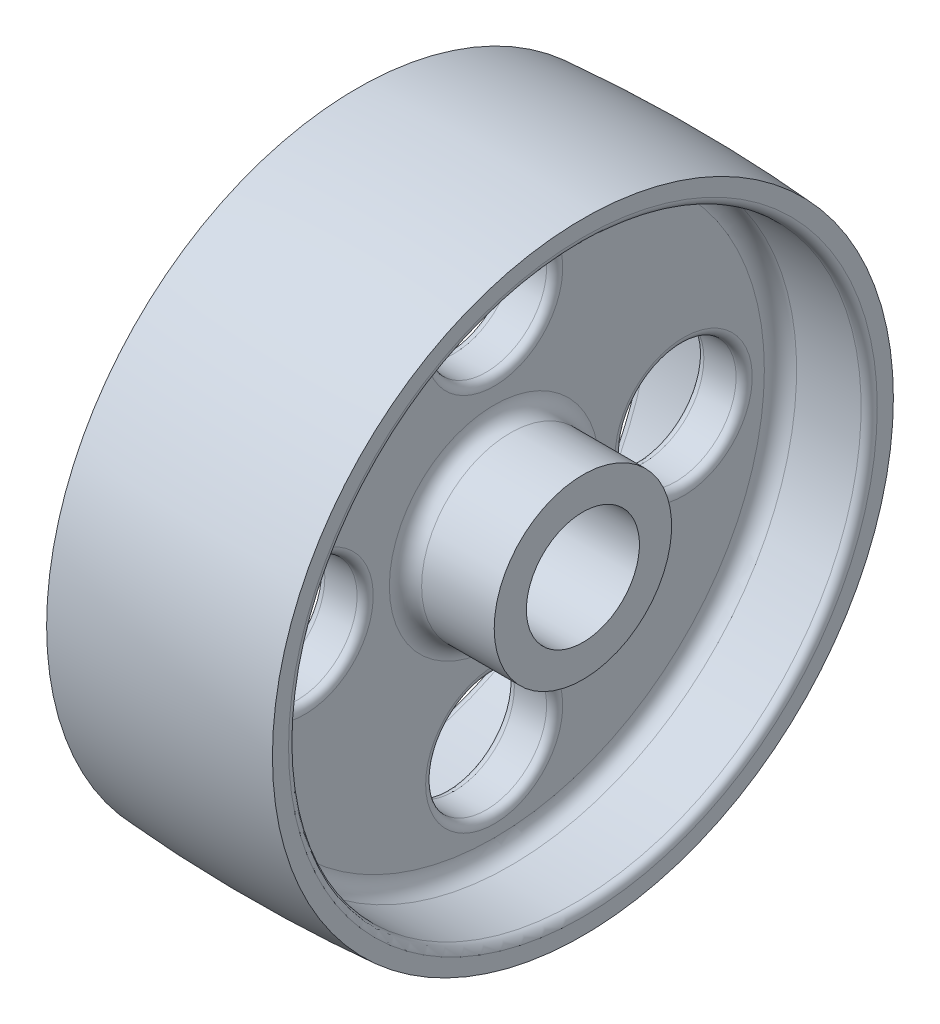
SolidWorks part; units mm, degrees
ref_plane "Front Plane" through (0, 0, 0) normal (0, 0, 1) x (1, 0, 0)
ref_plane "Top Plane" through (0, 0, 0) normal (0, 1, 0) x (1, 0, 0)
ref_plane "Right Plane" through (0, 0, 0) normal (1, 0, 0) x (0, 0, -1)
sketch "Sketch1" plane through (0, 0, 0) normal (0, 0, 1) x (1, 0, 0)
  line L0 (0, 0) -> (22.225, 0) construction
  line L2 (22.225, 11.1252) -> (22.225, 17.4625)
  line L3 (22.225, 17.4625) -> (7.9375, 17.4625)
  line L4 (4.7625, 20.6375) -> (4.7625, 53.1812)
  line L5 (7.9375, 56.3562) -> (20.6375, 56.3562)
  line L6 (22.225, 57.9438) -> (22.225, 61.1187)
  line L7 (0, 0) -> (0, 61.9125) construction
  line L8 (-22.225, 57.9438) -> (-22.225, 61.1187)
  line L9 (-7.9375, 56.3562) -> (-20.6375, 56.3562)
  line L10 (-4.7625, 20.6375) -> (-4.7625, 53.1812)
  line L11 (-22.225, 17.4625) -> (-7.9375, 17.4625)
  line L15 (-22.225, 11.1252) -> (22.225, 11.1252)
  line L17 (-22.225, 11.1252) -> (-22.225, 17.4625)
  arc A0 (-22.225, 61.1187) -> (22.225, 61.1187) centre (0, -249.6344) cw
  arc A1 (-7.9375, 56.3562) -> (-4.7625, 53.1812) centre (-7.9375, 53.1812) cw
  arc A2 (4.7625, 53.1812) -> (7.9375, 56.3562) centre (7.9375, 53.1812) cw
  arc A3 (7.9375, 17.4625) -> (4.7625, 20.6375) centre (7.9375, 20.6375) cw
  arc A4 (-4.7625, 20.6375) -> (-7.9375, 17.4625) centre (-7.9375, 20.6375) cw
  arc A5 (20.6375, 56.3562) -> (22.225, 57.9438) centre (20.6375, 57.9437) ccw
  arc A6 (-22.225, 57.9438) -> (-20.6375, 56.3562) centre (-20.6375, 57.9437) ccw
  point P16 (0, 0)
  point P20 (-4.7625, 56.3562)
  point P23 (4.7625, 56.3562)
  point P26 (4.7625, 17.4625)
  point P29 (-4.7625, 17.4625)
  point P34 (22.225, 56.3562)
  point P37 (-22.225, 56.3562)
  dimension "D8" = 3.175
  dimension "D11" = 1.5875
  dimension "D1" = 22.225
  dimension "D2" = 11.1252
  dimension "D3" = 17.4625
  dimension "D4" = 9.525
  dimension "D5" = 61.9125
  dimension "D6" = 0.7937
  dimension "D7" = 4.7625
revolve "Revolve1" add sketch "Sketch1" angle 360 about L0
sketch "Sketch2" plane through (0, 0, 0) normal (1, 0, 0) x (0, 0, -1)
  line L0 (0, 61.9125) -> (0, -61.9125) construction
  circle A0 centre (0, 0) radius 61.9125 construction
  circle A1 centre (0, 37.3062) radius 11.9063
  circle A3 centre (37.3062, 0) radius 11.9063
  circle A4 centre (0, -37.3062) radius 11.9063
  circle A5 centre (-37.3062, 0) radius 11.9063
  circle A6 centre (0, 0) radius 37.3063
  circle A7 centre (0, -37.3062) radius 16.2719 construction
  point P19 (0, 0)
  dimension "D1" = 23.8125
  dimension "D2" = 74.6125
  dimension "D4" = 32.5437
  dimension "D3" = 4
extrude "Cut-Extrude2" cut sketch "Sketch2" against normal up to next and the other way up to next contours A6 A4 | A4 A6 | A3 A6 | A6 A3 | A1 A6 | A6 A1 | A6 A5 | A5 A6
fillet "Fillet1" radius 1.5875 8 edges at (4.7625, 0, -25.4) (4.7625, -37.3062, 11.9063) (4.7625, 37.3062, 11.9063) (4.7625, 0, 49.2125) (-4.7625, 0, 25.4) (-4.7625, -37.3062, -11.9063) (-4.7625, 0, -49.2125) (-4.7625, 37.3062, -11.9063)
